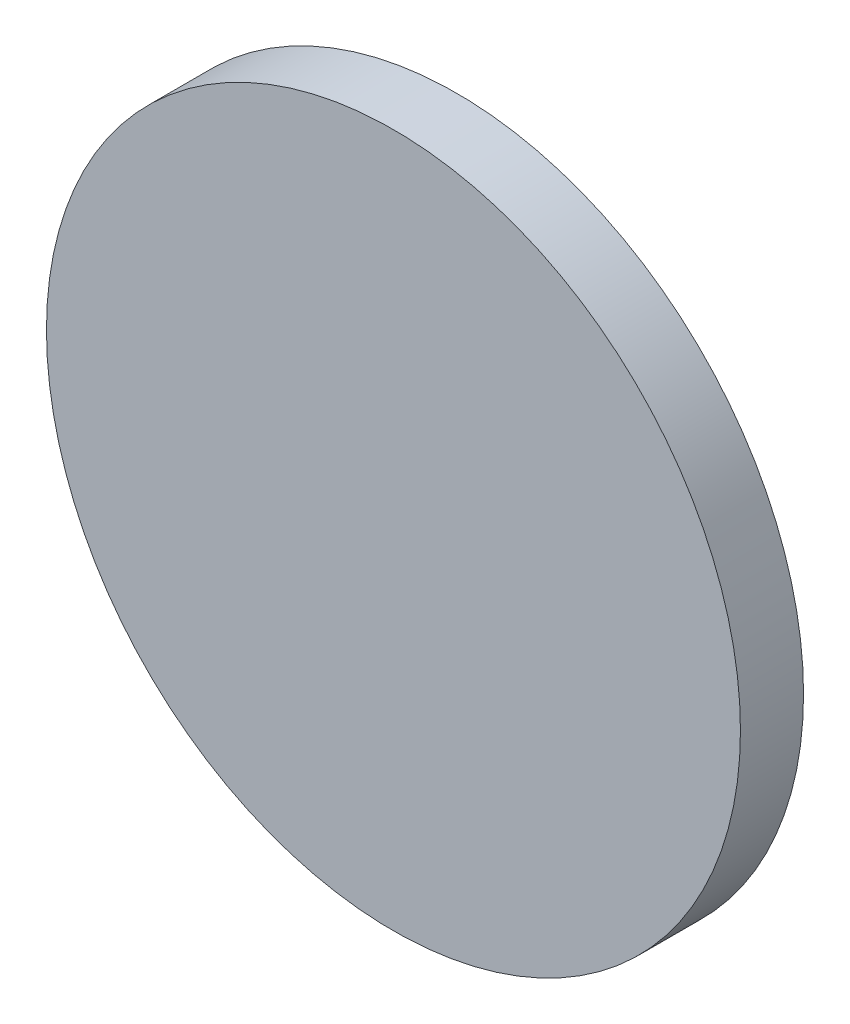
SolidWorks part; units mm, degrees
ref_plane "Front Plane" through (0, 0, 0) normal (0, 0, 1) x (1, 0, 0)
ref_plane "Top Plane" through (0, 0, 0) normal (0, 1, 0) x (1, 0, 0)
ref_plane "Right Plane" through (0, 0, 0) normal (1, 0, 0) x (0, 0, -1)
sketch "Sketch1" plane through (0, 0, 0) normal (0, 0, 1) x (1, 0, 0)
  circle A0 centre (0, 0) radius 11
  dimension "D1" = 22
extrude "Boss-Extrude1" add sketch "Sketch1" along normal blind 2
